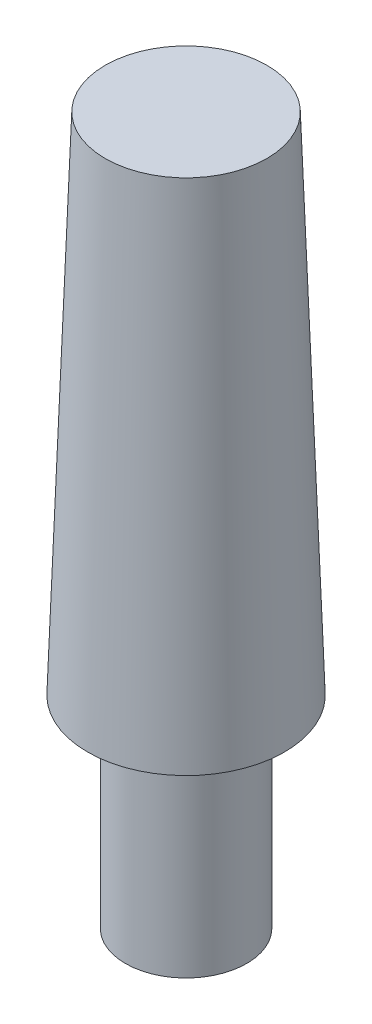
SolidWorks part; units mm, degrees
ref_plane "Front Plane" through (0, 0, 0) normal (0, 0, 1) x (1, 0, 0)
ref_plane "Top Plane" through (0, 0, 0) normal (0, 1, 0) x (1, 0, 0)
ref_plane "Right Plane" through (0, 0, 0) normal (1, 0, 0) x (0, 0, -1)
sketch "Sketch1" plane through (0, 0, 0) normal (0, 1, 0) x (1, 0, 0)
  circle A0 centre (0, 0) radius 3
  circle A1 centre (0, 0) radius 1
  dimension "D1" = 6
  dimension "D2" = 2
extrude "Boss-Extrude1" add sketch "Sketch1" along normal blind 10
sketch "Sketch2" plane through (0, 10, 0) normal (0, 1, 0) x (1, 0, 0)
  circle A0 centre (0, 0) radius 4
  dimension "D1" = 8
extrude "Boss-Extrude2" add sketch "Sketch2" along normal blind 10
sketch "Sketch3" plane through (0, 20, 0) normal (0, 1, 0) x (1, 0, 0)
  circle A0 centre (0, 0) radius 4
  dimension "D1" = 8
extrude "Boss-Extrude3" add sketch "Sketch3" along normal blind 15
draft "Draft1" type of draft neutral plane draft angle 2 faces to draft 1 face at (0, 10, 4) neutral plane through (0, 35, 0) neutral plane normal (0, 1, 0) parameters "D1"=2
